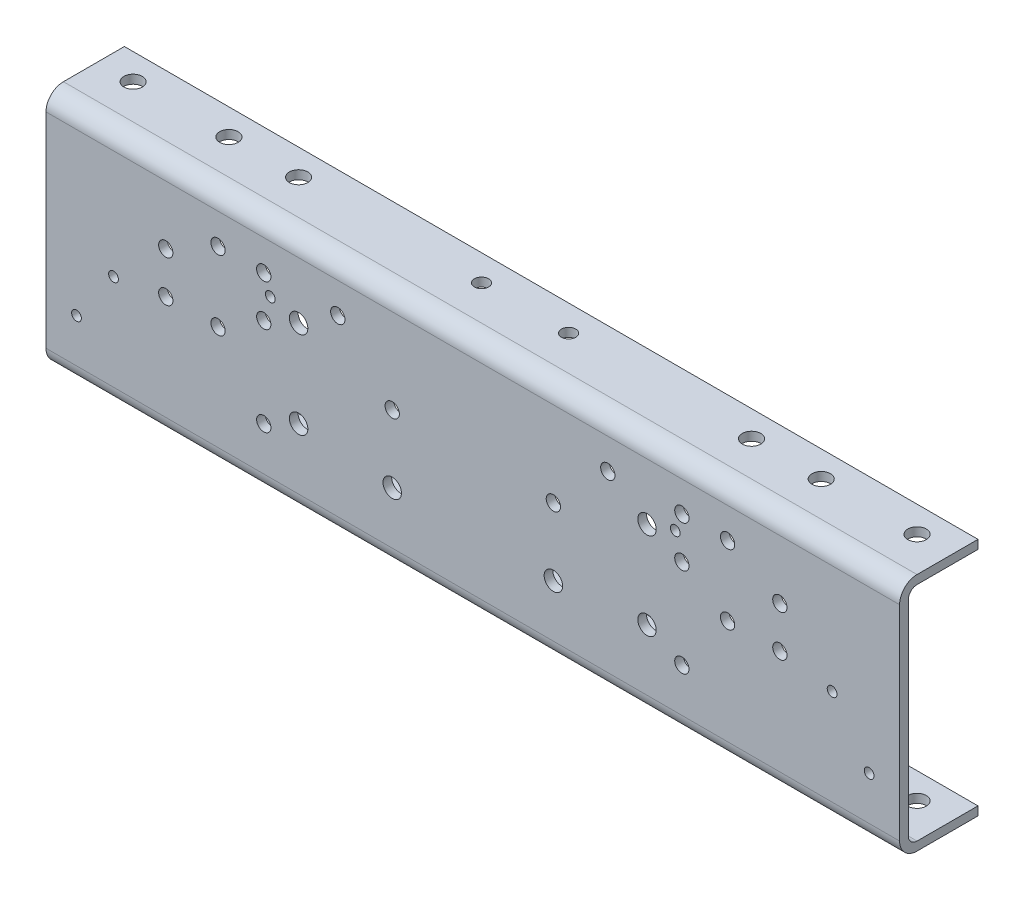
SolidWorks part; units mm, degrees
material "ASTM A36"
ref_plane "Front" through (0, 0, 0) normal (0, 0, 1) x (1, 0, 0)
ref_plane "Top" through (0, 0, 0) normal (0, 1, 0) x (1, 0, 0)
ref_plane "Side" through (0, 0, 0) normal (1, 0, 0) x (0, 0, -1)
sketch "Sketch1" plane through (0, 0, 0) normal (1, 0, 0) x (0, 0, -1)
  line L0 (57.15, 87.3125) -> (12.7, 87.3125)
  line L1 (0, 74.6125) -> (0, -74.6125)
  line L2 (12.7, -87.3125) -> (57.15, -87.3125)
  line L3 (57.15, -87.3125) -> (57.15, -80.9625)
  line L4 (57.15, -80.9625) -> (12.7, -80.9625)
  line L5 (6.35, -74.6125) -> (6.35, 74.6125)
  line L6 (12.7, 80.9625) -> (57.15, 80.9625)
  line L7 (57.15, 80.9625) -> (57.15, 87.3125)
  arc A0 (12.7, 87.3125) -> (0, 74.6125) centre (12.7, 74.6125) ccw
  arc A1 (0, -74.6125) -> (12.7, -87.3125) centre (12.7, -74.6125) ccw
  arc A2 (12.7, -80.9625) -> (6.35, -74.6125) centre (12.7, -74.6125) cw
  arc A3 (6.35, 74.6125) -> (12.7, 80.9625) centre (12.7, 74.6125) cw
  dimension "D4" = 6.35
  dimension "D1" = 6.35
  dimension "D2" = 57.15
  dimension "D3" = 174.625
extrude "Extrude1" add sketch "Sketch1" along normal mid plane 622.3
sketch "Sketch2" plane through (0, 0, 0) normal (0, 0, 1) x (1, 0, 0)
  line L0 (0, 62.5223) -> (0, -87.3125) construction
  line L1 (58.7375, -36.5125) -> (58.7375, 12.7) construction
  line L5 (127, -30.1625) -> (127, 33.3375) construction
  line L12 (288.925, -42.8625) -> (152.4, -42.8625) construction
  line L17 (185.7375, 1.5875) -> (185.7375, 52.3875) construction
  line L18 (185.7375, 52.3875) -> (98.425, 52.3875) construction
  line L20 (50, 0) -> (-50, 0) construction
  line L25 (0, -50) -> (0, 50) construction
  circle A1 centre (-185.7375, 52.3875) radius 5.207
  circle A3 centre (-261.9375, -4.7625) radius 3.556
  circle A4 centre (-288.925, -42.8625) radius 3.556
  circle A5 centre (-152.4, -42.8625) radius 5.207
  circle A6 centre (-127, -30.1625) radius 6.731
  circle A7 centre (-127, 33.3375) radius 6.731
  circle A8 centre (-98.425, 52.3875) radius 5.207
  circle A9 centre (-58.7375, 12.7) radius 5.207
  circle A10 centre (-58.7375, -36.5125) radius 6.731
  circle A11 centre (-185.7375, 1.5875) radius 5.207
  circle A13 centre (-147.6375, 39.6875) radius 3.556
  circle A14 centre (147.6375, 39.6875) radius 3.556
  circle A36 centre (98.425, 52.3875) radius 5.207
  circle A37 centre (127, 33.3375) radius 6.731
  circle A39 centre (185.7375, 52.3875) radius 5.207
  circle A41 centre (185.7375, 1.5875) radius 5.207
  circle A42 centre (261.9375, -4.7625) radius 3.556
  circle A43 centre (288.925, -42.8625) radius 3.556
  circle A44 centre (152.4, -42.8625) radius 5.207
  circle A45 centre (127, -30.1625) radius 6.731
  circle A46 centre (58.7375, 12.7) radius 5.207
  circle A47 centre (58.7375, -36.5125) radius 6.731
  point P3 (0, -87.3125)
other "AlignGroup4" parameters "D25"=7.112, "D26"=10.414, "D27"=13.462, "D30"=7.112, "D17"=13.462, "D18"=10.414, "D19"=7.112, "D20"=10.414, "D21"=7.112, "D14"=10.414, "D15"=7.112, "D22"=13.462, "D23"=13.462, "D24"=13.462, "D1"=0, "D2"=61.9125, "D3"=52.3875, "D4"=12.7, "D5"=1.5875, "D6"=12.7, "D7"=52.3875, "D8"=0, "D9"=58.7375, "D10"=98.425, "D11"=127, "D12"=152.4, "D13"=185.7375, "D16"=288.925, "D28"=36.5125, "D29"=12.7, "D31"=31.75, "D32"=120.65, "D33"=139.7
extrude "Cut-Web Holes" cut sketch "Sketch2" against normal through all
sketch "Sketch3" plane through (0, 0, 0) normal (0, 1, 0) x (1, 0, 0)
  line L0 (-165.1, 38.1) -> (-31.75, 38.1) construction
  line L1 (-31.75, 38.1) -> (31.75, 38.1) construction
  line L2 (31.75, 38.1) -> (165.1, 38.1) construction
  line L3 (-50, 0) -> (50, 0) construction
  line L4 (0, -50) -> (0, 50) construction
  line L5 (-311.15, 57.15) -> (-311.15, 12.7) construction
  line L7 (-215.9, 38.1) -> (-285.75, 38.1) construction
  line L8 (0, 0) -> (0, 40.7701) construction
  circle A0 centre (-285.75, 38.1) radius 6.731
  circle A1 centre (-215.9, 38.1) radius 6.731
  circle A2 centre (285.75, 38.1) radius 6.731
  circle A3 centre (215.9, 38.1) radius 6.731
  circle A4 centre (165.1, 38.1) radius 6.731
  circle A5 centre (31.75, 38.1) radius 5.207
  circle A6 centre (-31.75, 38.1) radius 5.207
  circle A7 centre (-165.1, 38.1) radius 6.731
other "AlignGroup1" parameters "D7"=10.414, "D8"=13.462, "D1"=100, "D2"=0, "D3"=31.75, "D4"=165.1, "D5"=31.75, "D6"=165.1, "D9"=311.15, "D10"=215.9, "D11"=285.75, "D12"=100
extrude "Cut-Flg Holes" cut sketch "Sketch3" along normal through all and the other way through all
sketch "Sketch6" plane through (0, 0, 0) normal (0, 0, 1) x (1, 0, 0)
  line L0 (0, 62.5223) -> (0, -87.3125) construction
  line L1 (311.15, 74.6125) -> (311.15, -74.6125) construction
  line L2 (311.15, -87.3125) -> (-311.15, -87.3125) construction
  circle A0 centre (-152.4, 52.3875) radius 5.207
  circle A2 centre (-223.8375, 31.75) radius 5.207
  circle A6 centre (-152.4, 22.225) radius 5.207
  circle A9 centre (-223.8375, 1.5875) radius 5.207
  circle A12 centre (223.8375, 1.5875) radius 5.207
  circle A15 centre (152.4, 22.225) radius 5.207
  circle A38 centre (152.4, 52.3875) radius 5.207
  circle A40 centre (223.8375, 31.75) radius 5.207
  point P3 (0, -87.3125)
  dimension "D27" = 20.6375
  dimension "D20" = 20.6375
  dimension "D14" = 71.4375
  dimension "D5" = 87.3125
  dimension "D6" = 10.414
  dimension "D3" = 119.0625
  dimension "D4" = 0
  dimension "D28" = 88.9
extrude "VLV-MODULATOR" cut sketch "Sketch6" against normal through all
